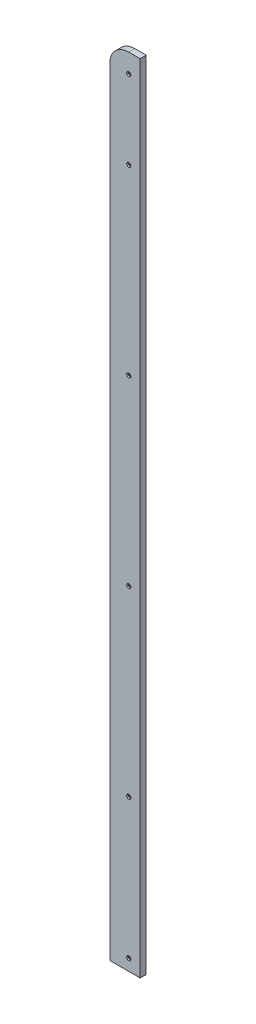
SolidWorks part; units mm, degrees
ref_plane "Plan de face" through (0, 0, 0) normal (0, 0, 1) x (1, 0, 0)
ref_plane "Plan de dessus" through (0, 0, 0) normal (0, 1, 0) x (1, 0, 0)
ref_plane "Plan de droite" through (0, 0, 0) normal (1, 0, 0) x (0, 0, -1)
sketch "Esquisse1" plane through (0, 0, 0) normal (0, 0, 1) x (1, 0, 0)
  line L0 (201, 23.5) -> (201, 0) construction
  line L1 (201, 18.5) -> (186, 18.5)
  line L2 (201, 18.5) -> (201, -1029)
  line L3 (201, -1029) -> (161, -1029)
  line L4 (161, -6.5) -> (161, -1029)
  line L5 (201, -1029) -> (-162, -1029) construction
  line L6 (-261, 18.5) -> (-187, 18.5) construction
  arc A0 (186, 18.5) -> (161, -6.5) centre (186, -6.5) ccw
  dimension "D2" = 25
  dimension "D1" = 40
extrude "Boss.-Extru.1" add sketch "Esquisse1" along normal blind 8 contours L4 L3 L2 L1 A0
hole_wizard "Chambrage pour vis à tête cylindrique courte six pans creux M31" positions "Esquisse2" profile "Esquisse3" counterbore size "M3" standard "DIN" end condition through all
sketch "Esquisse2" plane through (0, 0, 8) normal (0, 0, 1) x (1, 0, 0)
  line L0 (201, 18.5) -> (201, -1029) construction
  line L1 (201, -1029) -> (161, -1029) construction
  line L2 (-181, -980) -> (181, -980) construction
  line L3 (186, -830) -> (186, -590) construction
  line L4 (186, -590) -> (186, -350) construction
  line L5 (186, -350) -> (186, -110) construction
  line L7 (201, 18.5) -> (186, 18.5) construction
  point P0 (186, -1014)
  point P2 (186, -830)
  point P4 (186, -590)
  point P6 (186, -350)
  point P8 (186, -110)
  point P10 (186, -6.5)
  dimension "D1" = 15
  dimension "D2" = 15
  dimension "D3" = 150
  dimension "D4" = 240
  dimension "D5" = 25
sketch "Esquisse3" plane through (186, -1014, 8) normal (1, 0, 0) x (0, -1, 0)
  line L0 (0, 0) -> (0, 8)
  line L1 (0, 8) -> (1.5, 8)
  line L3 (1.5, 8) -> (1.5, 2)
  line L4 (1.5, 2) -> (2.75, 2)
  line L5 (2.75, 2) -> (2.75, 0)
  line L7 (2.75, 0) -> (0, 0)
  line L11 (0, -6.35) -> (0, 107.95) construction
  dimension "Diamètre du perçage jusqu'au prochain" = 3
  dimension "Profondeur du perçage jusqu'au prochain" = 8
  dimension "Diamètre du chambrage" = 5.5
  dimension "Profondeur du chambrage" = 2
